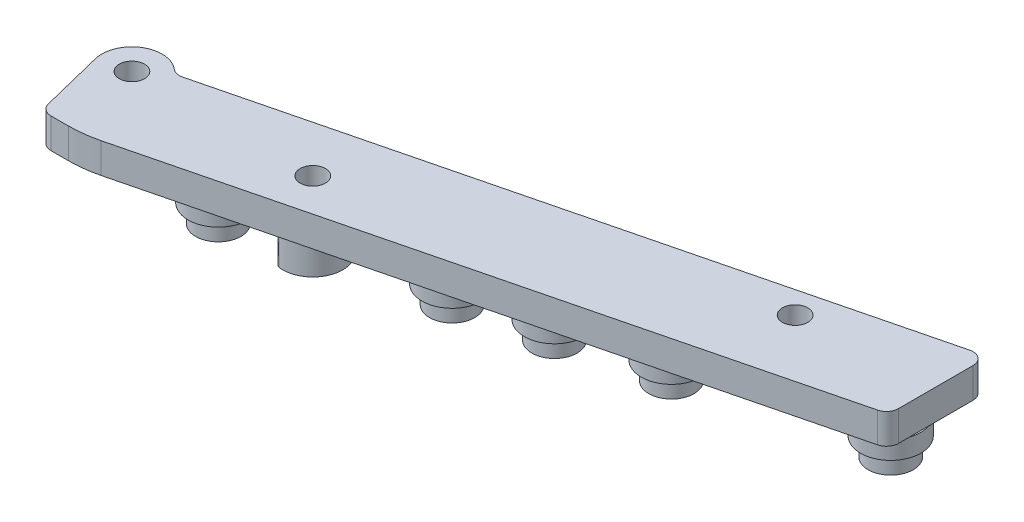
SolidWorks part; units mm, degrees
ref_plane "Front Plane" through (0, 0, 0) normal (0, 0, 1) x (1, 0, 0)
ref_plane "Top Plane" through (0, 0, 0) normal (0, 1, 0) x (1, 0, 0)
ref_plane "Right Plane" through (0, 0, 0) normal (1, 0, 0) x (0, 0, -1)
sketch "Sketch1" plane through (0, 0, 0) normal (0, 1, 0) x (-1, 0, 0)
  line L0 (27.94, 12.7851) -> (25.619, 22.0941) construction
  line L2 (132.8591, 54.0676) -> (1.9255, 21.4222)
  line L4 (137.8622, 47.4617) -> (6.0087, 14.5869) construction
  line L5 (3.1545, 0.7865) -> (135.8682, 33.8757)
  line L7 (148.4014, 39.7213) -> (145.1164, 52.8965)
  line L8 (148.4824, 37.0208) -> (398.1253, 99.2638)
  line L9 (0, 18.9576) -> (0, 3.2511)
  line L10 (139.0039, 54.8221) -> (142.6519, 54.8221)
  circle A0 centre (42.977, 23.8042) radius 11.1125 construction
  circle A1 centre (79.9452, 33.0214) radius 11.1125 construction
  circle A2 centre (119.3781, 42.8531) radius 11.1125 construction
  circle A3 centre (6.0087, 14.5869) radius 11.1125 construction
  circle A7 centre (142.24, 38.1851) radius 2.667
  circle A8 centre (27.94, 12.7851) radius 2.667
  circle A9 centre (104.14, 38.1851) radius 2.667
  arc A11 (138.1276, 33.3466) -> (148.4014, 39.7213) centre (142.24, 38.1851) ccw
  arc A15 (135.8682, 33.8757) -> (138.1276, 33.3466) centre (136.4827, 31.4112) cw
  arc A16 (145.1164, 52.8965) -> (142.6519, 54.8221) centre (142.6519, 52.2821) ccw
  arc A17 (3.1545, 0.7865) -> (0, 3.2511) centre (2.54, 3.2511) cw
  arc A18 (0, 18.9576) -> (1.9255, 21.4222) centre (2.54, 18.9576) cw
  arc A19 (132.8591, 54.0676) -> (139.0039, 54.8221) centre (139.0039, 29.4221) cw
  point P19 (137.2749, 34.2265)
  point P27 (144.6363, 54.8221)
  point P33 (0, 0)
  point P37 (0, 20.9421)
  point P40 (135.8852, 54.8221)
  dimension "D1" = 19.05
  dimension "D5" = 38.1
  dimension "D6" = 22.225
  dimension "D9" = 12.7851
  dimension "D10" = 141.4774
  dimension "D11" = 12.7
  dimension "D12" = 5.334
  dimension "D13" = 6.35
  dimension "D14" = 140.0451
  dimension "D15" = 104.14
  dimension "D18" = 27.94
  dimension "D19" = 38.1851
  dimension "D20" = 2.54
  dimension "D21" = 25.4
  dimension "D22" = 5.08
  dimension "D3" = 40.64
  dimension "D4" = 38.1
  dimension "D7" = 104
  dimension "D8" = 7.62
  dimension "D16" = 8.7511
  dimension "D17" = 15.5631
extrude "Boss-Extrude1" add sketch "Sketch1" against normal blind 6.35
sketch "Sketch3" plane through (0, -6.35, 0) normal (0, -1, 0) x (-1, 0, 0)
  line L1 (6.0087, -14.5869) -> (119.3781, -42.8531) construction
  line L4 (0, 55) -> (0, -55) construction
  line L13 (-55, 0) -> (55, 0) construction
  circle A20 centre (6.0087, -14.5869) radius 11.1125 construction
  circle A21 centre (119.3781, -42.8531) radius 11.1125 construction
  circle A22 centre (79.9452, -33.0214) radius 11.1125 construction
  circle A23 centre (42.977, -23.8042) radius 11.1125 construction
  circle A33 centre (6.0087, -14.5869) radius 6.35
  circle A34 centre (42.977, -23.8042) radius 6.35
  circle A35 centre (79.9452, -33.0214) radius 6.35
  circle A36 centre (119.3781, -42.8531) radius 6.35
  circle A37 centre (62.6934, -28.72) radius 6.35
  dimension "D1" = 38.1
  dimension "D5" = 14.5869
  dimension "D6" = 14
  dimension "D7" = 12.7
  dimension "D2" = 38.1
  dimension "D3" = 40.64
  dimension "D4" = 6.0087
extrude "Boss-Extrude2" add sketch "Sketch3" along normal blind 3.81
sketch "Sketch4" plane through (0, -10.16, 0) normal (0, -1, 0) x (1, 0, 0)
  circle A0 centre (-6.0087, 14.5869) radius 4.7625
  circle A1 centre (-42.977, 23.8042) radius 4.7625
  circle A2 centre (-62.6934, 28.72) radius 4.7625
  circle A3 centre (-79.9452, 33.0214) radius 4.7625
  circle A4 centre (-119.3781, 42.8531) radius 4.7625
  dimension "D1" = 9.525
extrude "Boss-Extrude3" add sketch "Sketch4" along normal blind 3.81
sketch "Sketch5" plane through (0, -6.35, 0) normal (0, -1, 0) x (1, 0, 0)
  line L0 (-105.5802, 43.778) -> (-105.7153, 41.5623)
  line L1 (-107.3366, 36.2697) -> (-108.4657, 34.3585)
  circle A4 centre (-142.24, 38.1851) radius 6.35
  arc A5 (-108.3101, 33.3962) -> (-104.9122, 44.4879) centre (-104.14, 38.1851) ccw
  circle A7 centre (-27.94, 12.7851) radius 5.08
  circle A9 centre (-104.14, 38.1851) radius 2.667 construction
  arc A10 (-106.116, 36.3939) -> (-104.7737, 40.7757) centre (-104.14, 38.1851) ccw
  circle A11 centre (-142.24, 38.1851) radius 2.667
  circle A13 centre (-27.94, 12.7851) radius 2.724
  arc A15 (-108.3101, 33.3962) -> (-108.4657, 34.3585) centre (-107.8097, 33.9709) cw
  arc A16 (-107.3366, 36.2697) -> (-106.116, 36.3939) centre (-106.6806, 35.8821) cw
  arc A17 (-104.7737, 40.7757) -> (-105.7153, 41.5623) centre (-104.9547, 41.5159) cw
  arc A18 (-104.9122, 44.4879) -> (-105.5802, 43.778) centre (-104.8196, 43.7316) ccw
  point P0 (-32.8691, 13.6789)
  point P35 (-106.6819, 37.3779)
  point P38 (-105.7937, 40.2775)
  dimension "D1" = 12.7
  dimension "D2" = 2.2157
  dimension "D4" = 1.778
  dimension "D3" = 1.778
  dimension "D7" = 0.762
  dimension "D6" = 5.334
  dimension "D9" = 10.16
  dimension "D11" = 5.4479
  dimension "D5" = 1.9112
extrude "Boss-Extrude4" add sketch "Sketch5" along normal up to surface (7.62 mm away) up to face at (-119.3781, -13.97, 38.0906)
